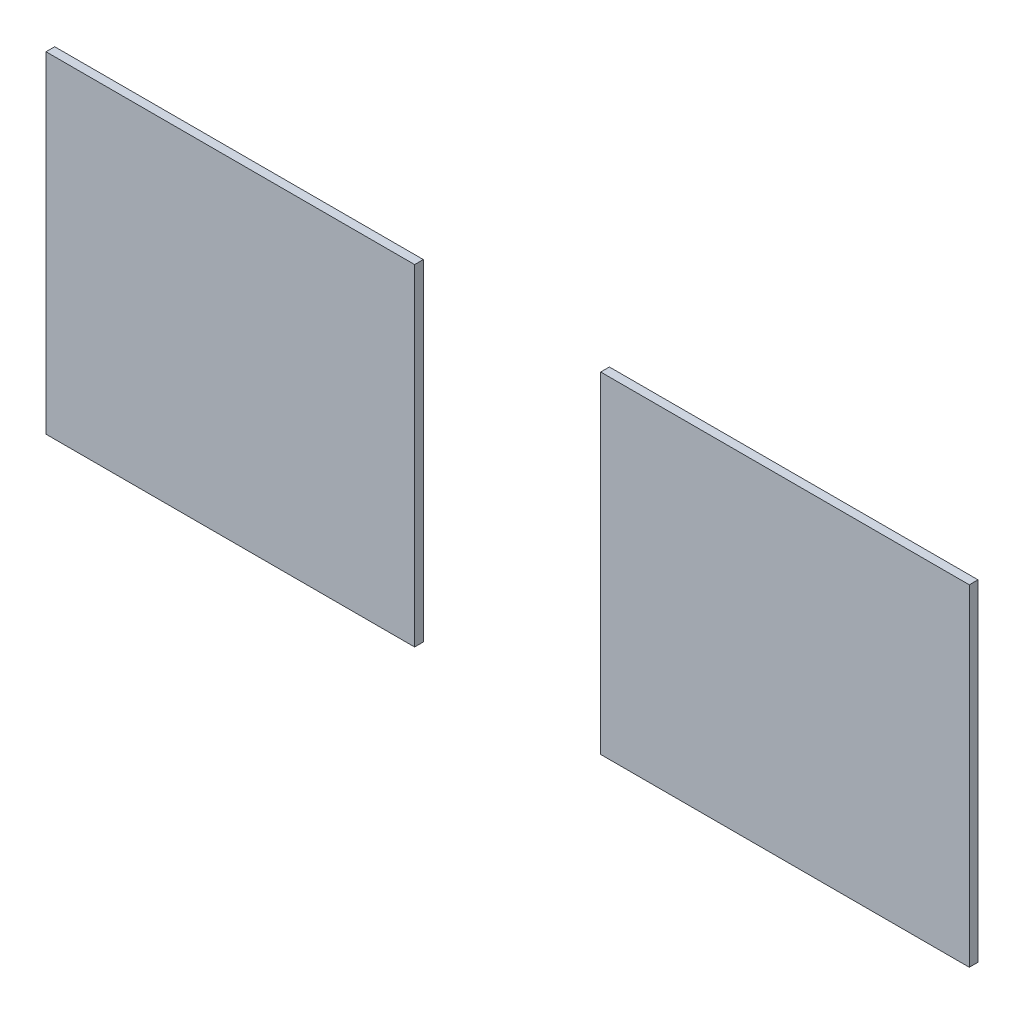
SolidWorks part; units mm, degrees
ref_plane "Plan de face" through (0, 0, 0) normal (0, 0, 1) x (1, 0, 0)
ref_plane "Plan de dessus" through (0, 0, 0) normal (0, 1, 0) x (1, 0, 0)
ref_plane "Plan de droite" through (0, 0, 0) normal (1, 0, 0) x (0, 0, -1)
sketch "Esquisse1" plane through (0, 0, 0) normal (0, 0, 1) x (1, 0, 0)
  line L1 (0, 0) -> (10.62, 0)
  line L2 (0, 0) -> (0, 3.81)
  line L3 (0, 3.81) -> (10.62, 3.81)
  line L4 (10.62, 0) -> (10.62, 3.81)
  dimension "D1" = 10.62
  dimension "D2" = 3.81
sketch "Esquisse2" plane through (0, 0, 0) normal (0, 0, 1) x (1, 0, 0)
  line L0 (0, 3.81) -> (10.62, 3.81) construction
  line L1 (0, 0) -> (4.24, 0)
  line L2 (0, 0) -> (0, 3.81)
  line L3 (0, 3.81) -> (4.24, 3.81)
  line L4 (4.24, 0) -> (4.24, 3.81)
  line L5 (0, 0) -> (10.62, 0) construction
  line L6 (10.62, 3.81) -> (6.38, 3.81)
  line L7 (10.62, 3.81) -> (10.62, 0)
  line L8 (10.62, 0) -> (6.38, 0)
  line L9 (6.38, 3.81) -> (6.38, 0)
  dimension "D1" = 4.24
  dimension "D2" = 4.24
extrude "Boss.-Extru.1" add sketch "Esquisse2" along normal blind 0.1
